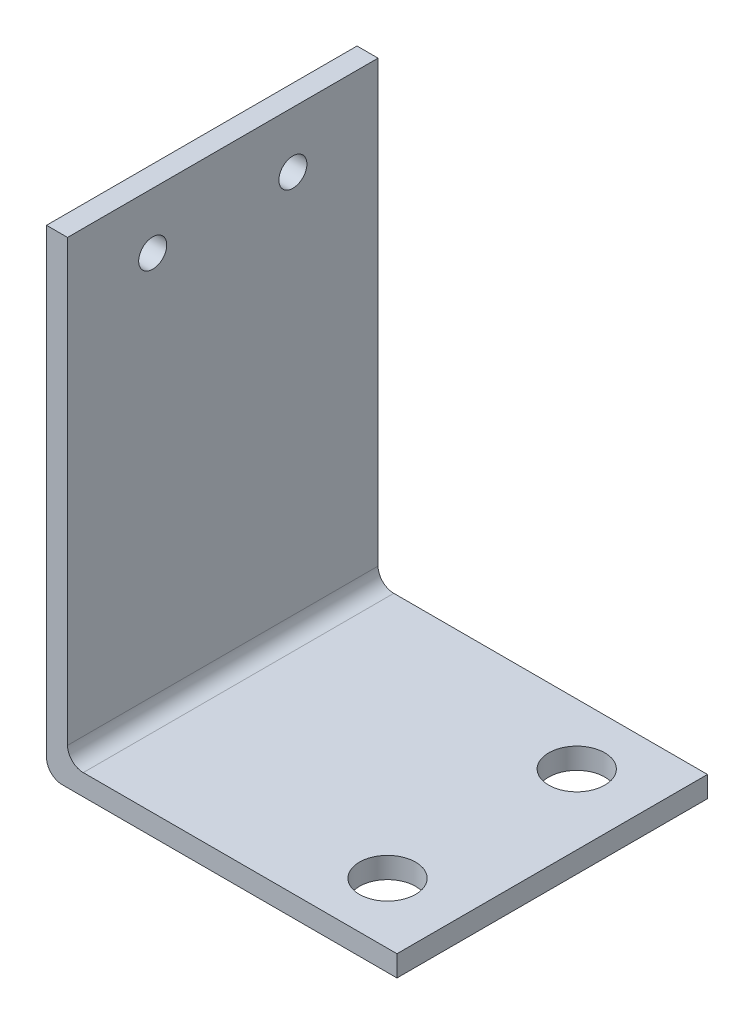
SolidWorks part; units mm, degrees
material "AISI 1020"
ref_plane "Plan de face" through (0, 0, 0) normal (0, 0, 1) x (1, 0, 0)
ref_plane "Plan de dessus" through (0, 0, 0) normal (0, 1, 0) x (1, 0, 0)
ref_plane "Plan de droite" through (0, 0, 0) normal (1, 0, 0) x (0, 0, -1)
sketch "Esquisse1" plane through (0, 0, 0) normal (0, 0, 1) x (1, 0, 0)
  line L0 (0, 1.1223) -> (0, 34)
  line L1 (1.1223, 0) -> (25, 0)
  line L2 (2.6223, 1.5) -> (25, 1.5)
  line L3 (1.5, 2.6223) -> (1.5, 34)
  line L4 (0, 34) -> (1.5, 34)
  line L5 (25, 0) -> (25, 1.5)
  line L6 (1.5, 1.5) -> (25, 1.5) construction
  line L7 (1.5, 1.5) -> (1.5, 34) construction
  line L8 (0, 0) -> (0, 34) construction
  line L9 (0, 0) -> (25, 0) construction
  arc A0 (2.6223, 1.5) -> (1.5, 2.6223) centre (2.6223, 2.6223) cw
  arc A1 (0, 1.1223) -> (1.1223, 0) centre (1.1223, 1.1223) ccw
  point P13 (0, 0)
  dimension "D4" = 1.1223
  dimension "D1" = 25
  dimension "D2" = 34
  dimension "D3" = 1.5
extrude "Boss.-Extru.1" add sketch "Esquisse1" along normal blind 22.15
sketch "Esquisse2" plane through (0, 1.5, 0) normal (0, 1, 0) x (1, 0, 0)
  line L0 (25, -22.15) -> (25, 0) construction
  line L1 (25, -11.075) -> (8.3358, -11.075) construction
  circle A0 centre (20, -4.325) radius 2
  circle A1 centre (20, -17.825) radius 2
  dimension "D2" = 4
  dimension "D1" = 13.5
  dimension "D3" = 5
  dimension "D4" = 6.75
extrude "Enlèv. mat.-Extru.1" cut sketch "Esquisse2" against normal through all
sketch "Esquisse3" plane through (1.5, 0, 0) normal (1, 0, 0) x (0, 0, -1)
  line L0 (-22.15, 34) -> (0, 34) construction
  line L1 (-11.075, 34) -> (-11.075, -4.9642) construction
  circle A0 centre (-16.075, 30) radius 1
  circle A1 centre (-6.075, 30) radius 1
  dimension "D3" = 2
  dimension "D1" = 10
  dimension "D2" = 4
  dimension "D4" = 5
extrude "Enlèv. mat.-Extru.2" cut sketch "Esquisse3" against normal through all
